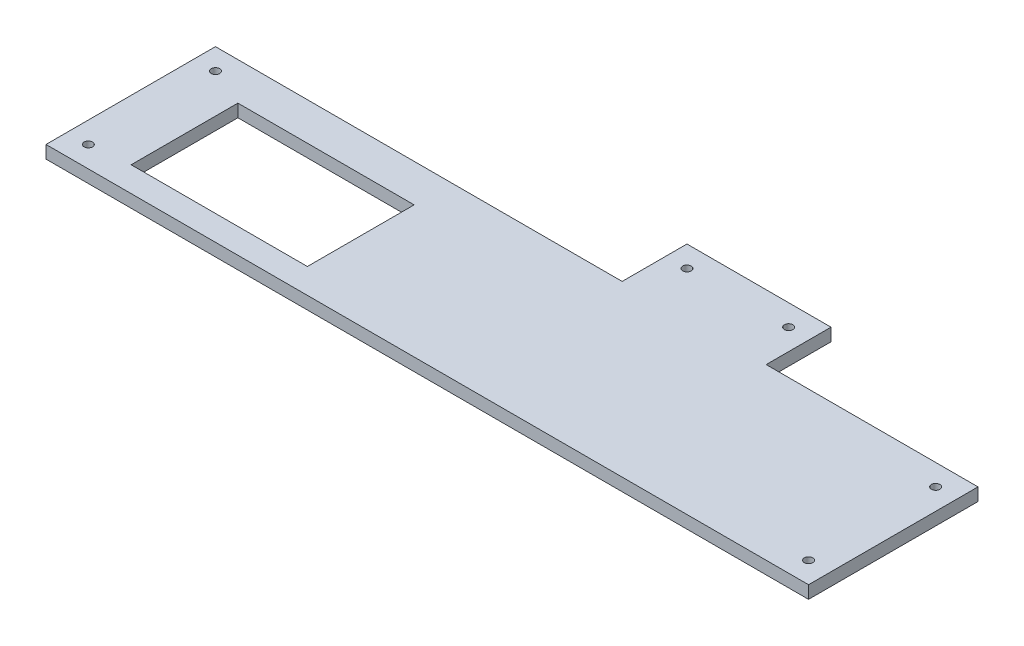
SolidWorks part; units mm, degrees
ref_plane "Front Plane" through (0, 0, 0) normal (0, 0, 1) x (1, 0, 0)
ref_plane "Top Plane" through (0, 0, 0) normal (0, 1, 0) x (1, 0, 0)
ref_plane "Right Plane" through (0, 0, 0) normal (1, 0, 0) x (0, 0, -1)
sketch "Sketch1" plane through (0, 0, 0) normal (0, 1, 0) x (1, 0, 0)
  line L0 (0, 0) -> (-450, 0) construction
  line L1 (0, 0) -> (0, 100) construction
  line L8 (450, 100) -> (-450, 100)
  line L9 (-450, 100) -> (-450, -100)
  line L10 (-450, -100) -> (450, -100)
  line L11 (450, -100) -> (450, 100)
  circle A4 centre (425, -75) radius 5
  circle A5 centre (425, 75) radius 5
  circle A6 centre (-425, -75) radius 5
  circle A7 centre (-425, 75) radius 5
  dimension "D4" = 25
  dimension "D1" = 900
  dimension "D2" = 200
  dimension "D3" = 25
extrude "Boss-Extrude1" add sketch "Sketch1" against normal blind 15
sketch "Sketch2" plane through (0, -15, 0) normal (0, -1, 0) x (1, 0, 0)
  line L1 (-379, 70.5) -> (-171, 70.5)
  line L2 (-379, 70.5) -> (-379, -55.5)
  line L3 (-379, -55.5) -> (-171, -55.5)
  line L4 (-171, 70.5) -> (-171, -55.5)
extrude "Shredder Opening" cut sketch "Sketch2" against normal through all
sketch "Sketch3" plane through (0, 0, 0) normal (0, 1, 0) x (1, 0, 0)
  line L0 (450, 100) -> (-450, 100) construction
  line L1 (200, 100) -> (30, 100)
  line L2 (200, 100) -> (200, 176.5)
  line L3 (200, 176.5) -> (30, 176.5)
  line L4 (30, 100) -> (30, 176.5)
  line L5 (180, -81.5) -> (180, 156.5) construction
  line L6 (50, 156.5) -> (180, 156.5) construction
  line L7 (50, -81.5) -> (50, 156.5) construction
  line L8 (115, 176.5) -> (115, 267.7218) construction
  circle A0 centre (175, 151.5) radius 5 construction
  circle A1 centre (175, 151.5) radius 5
  circle A2 centre (55, 151.5) radius 5
  dimension "D1" = 20
  dimension "D2" = 20
  dimension "D3" = 20
extrude "Legs add on" add sketch "Sketch3" against normal through all
